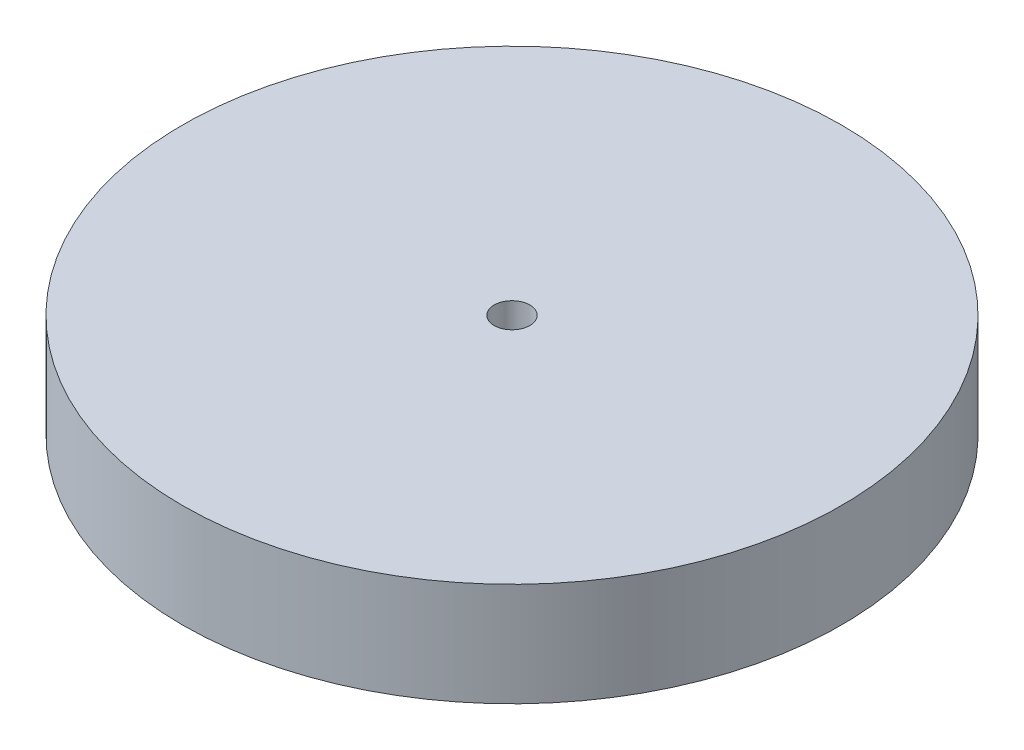
SolidWorks part; units mm, degrees
ref_plane "Front Plane" through (0, 0, 0) normal (0, 0, 1) x (1, 0, 0)
ref_plane "Top Plane" through (0, 0, 0) normal (0, 1, 0) x (1, 0, 0)
ref_plane "Right Plane" through (0, 0, 0) normal (1, 0, 0) x (0, 0, -1)
sketch "Sketch1" plane through (0, 0, 0) normal (0, 1, 0) x (1, 0, 0)
  circle A0 centre (0, 0) radius 60.5
  dimension "D1" = 121
extrude "Boss-Extrude1" add sketch "Sketch1" along normal blind 19
sketch "Sketch2" plane through (0, 19, 0) normal (0, 1, 0) x (1, 0, 0)
  circle A0 centre (0, 0) radius 3.275
  dimension "D1" = 6.55
extrude "Cut-Extrude2" cut sketch "Sketch2" against normal through all
